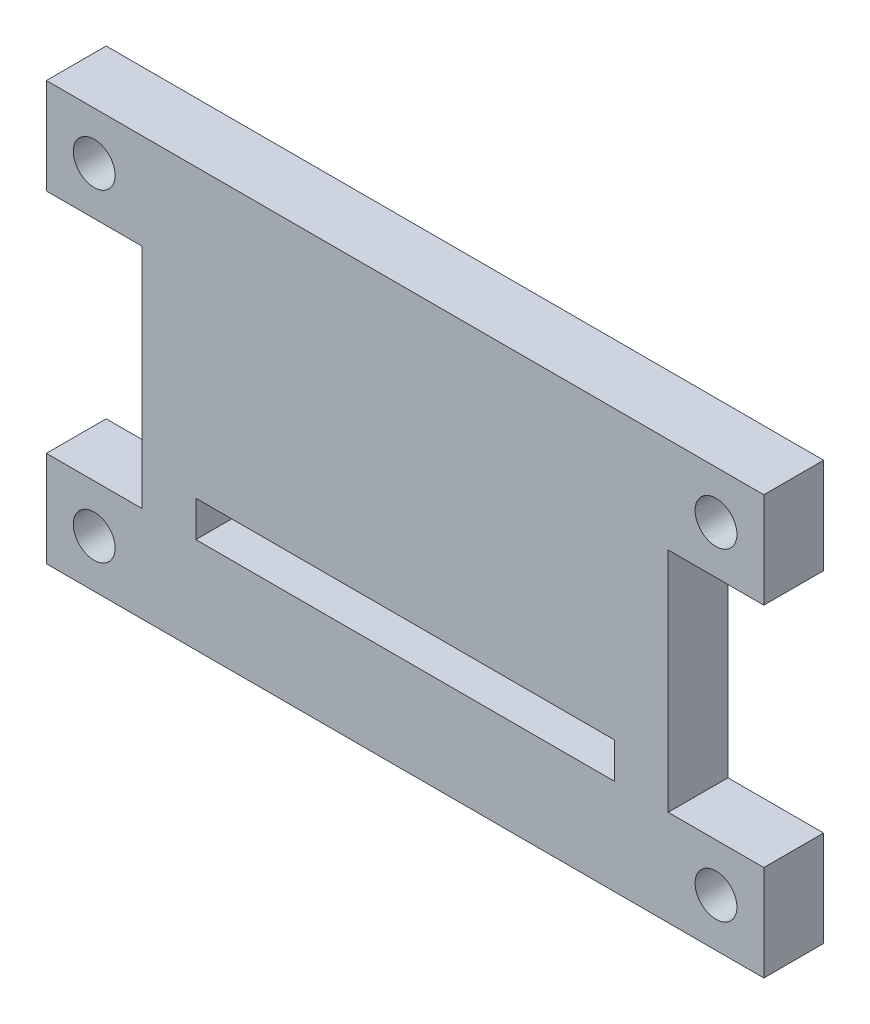
SolidWorks part; units mm, degrees
ref_plane "前基準面" through (0, 0, 0) normal (0, 0, 1) x (1, 0, 0)
ref_plane "上基準面" through (0, 0, 0) normal (0, 1, 0) x (1, 0, 0)
ref_plane "右基準面" through (0, 0, 0) normal (1, 0, 0) x (0, 0, -1)
sketch "草圖1" plane through (0, 0, 0) normal (0, 0, 1) x (1, 0, 0)
  line L1 (-22, 17.5) -> (22, 17.5)
  line L2 (-22, 17.5) -> (-22, -17.5)
  line L3 (-22, -17.5) -> (22, -17.5)
  line L4 (22, 17.5) -> (22, -17.5)
  line L5 (-22, 17.5) -> (22, -17.5) construction
  line L6 (-22, -17.5) -> (22, 17.5) construction
  line L7 (-30, 9.5) -> (-22, 9.5)
  line L8 (-30, 9.5) -> (-30, 17.5)
  line L9 (-30, 17.5) -> (-22, 17.5)
  line L10 (-22, 9.5) -> (-22, 17.5)
  line L11 (-30, 9.5) -> (-22, 17.5) construction
  line L12 (-30, 17.5) -> (-22, 9.5) construction
  line L13 (-30, -9.5) -> (-22, -9.5)
  line L14 (-30, -9.5) -> (-30, -17.5)
  line L15 (-30, -17.5) -> (-22, -17.5)
  line L16 (-22, -9.5) -> (-22, -17.5)
  line L17 (-30, -9.5) -> (-22, -17.5) construction
  line L18 (-30, -17.5) -> (-22, -9.5) construction
  line L19 (30, 9.5) -> (22, 9.5)
  line L20 (30, 9.5) -> (30, 17.5)
  line L21 (30, 17.5) -> (22, 17.5)
  line L22 (22, 9.5) -> (22, 17.5)
  line L23 (30, 9.5) -> (22, 17.5) construction
  line L24 (30, 17.5) -> (22, 9.5) construction
  line L25 (30, -9.5) -> (22, -9.5)
  line L26 (30, -9.5) -> (30, -17.5)
  line L27 (30, -17.5) -> (22, -17.5)
  line L28 (22, -9.5) -> (22, -17.5)
  line L29 (30, -9.5) -> (22, -17.5) construction
  line L30 (30, -17.5) -> (22, -9.5) construction
  circle A0 centre (-26, 13.5) radius 1.75
  circle A1 centre (26, 13.5) radius 1.75
  circle A2 centre (26, -13.5) radius 1.75
  circle A3 centre (-26, -13.5) radius 1.75
  point P0 (0, 0)
  point P6 (-26, 13.5)
  point P7 (-26, -13.5)
  point P11 (26, 13.5)
  point P15 (26, -13.5)
  dimension "D4" = 3.5
  dimension "D1" = 8
  dimension "D2" = 44
  dimension "D3" = 35
extrude "填料-伸長1" add sketch "草圖1" along normal blind 5 contours L9 L8 L7 L2 | L20 L21 L4 L19 | L27 L26 L25 L4 | L14 L15 L2 L13 | L4 L1 L2 L3
sketch "草圖2" plane through (0, 0, 5) normal (0, 0, 1) x (1, 0, 0)
  line L0 (0, -2.75) -> (0, 2.75) construction
  line L1 (-17.5, -6.5) -> (17.5, -6.5)
  line L2 (-17.5, -6.5) -> (-17.5, -9.5)
  line L3 (-17.5, -9.5) -> (17.5, -9.5)
  line L4 (17.5, -6.5) -> (17.5, -9.5)
  line L5 (-17.5, -6.5) -> (17.5, -9.5) construction
  line L6 (-17.5, -9.5) -> (17.5, -6.5) construction
  line L7 (30, -9.5) -> (22, -9.5) construction
  point P0 (0, -8)
  dimension "D1" = 3
  dimension "D2" = 35
extrude "除料-伸長1" cut sketch "草圖2" against normal up to next
